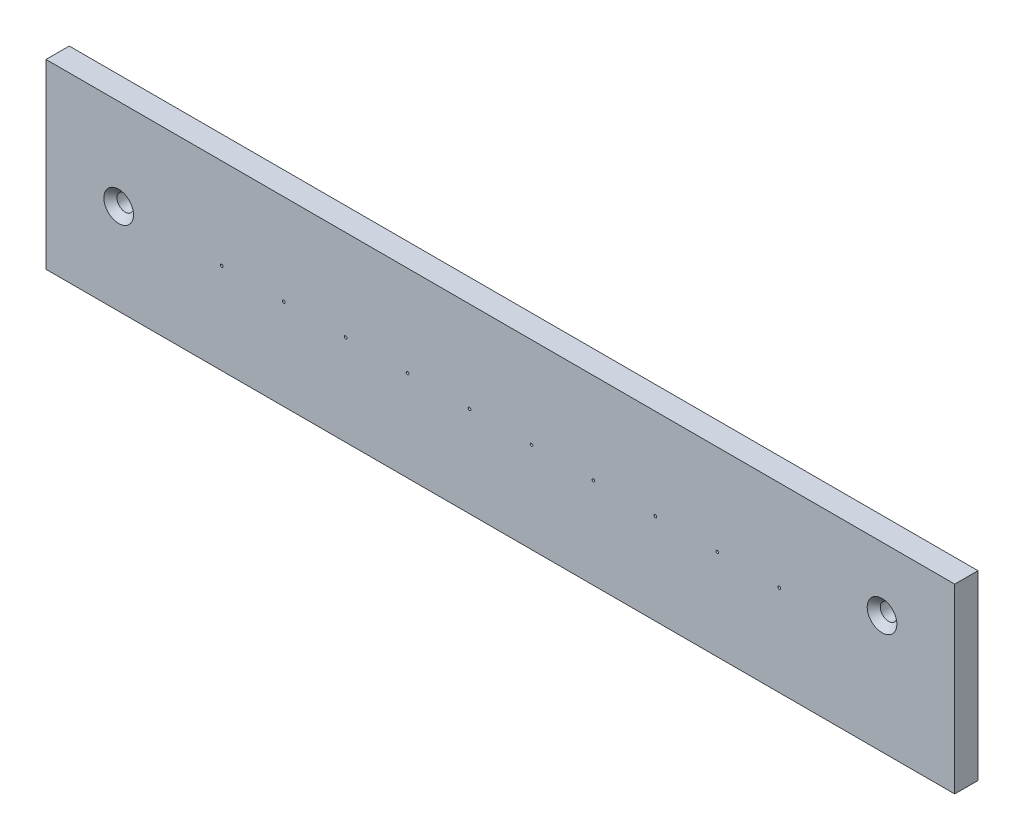
SolidWorks part; units mm, degrees
ref_plane "Front Plane" through (0, 0, 0) normal (0, 0, 1) x (1, 0, 0)
ref_plane "Top Plane" through (0, 0, 0) normal (0, 1, 0) x (1, 0, 0)
ref_plane "Right Plane" through (0, 0, 0) normal (1, 0, 0) x (0, 0, -1)
sketch "Sketch1" plane through (0, 0, 0) normal (0, 0, 1) x (1, 0, 0)
  line L1 (-31.6476, 20.0742) -> (127.1024, 20.0742)
  line L2 (-31.6476, 20.0742) -> (-31.6476, -11.6758)
  line L3 (-31.6476, -11.6758) -> (127.1024, -11.6758)
  line L4 (127.1024, 20.0742) -> (127.1024, -11.6758)
  dimension "D1" = 31.75
  dimension "D2" = 158.75
extrude "Boss-Extrude1" add sketch "Sketch1" against normal blind 4.064
sketch "Sketch2" plane through (0, 0, 0) normal (0, 0, 1) x (1, 0, 0)
  line L0 (-31.6476, 20.0742) -> (-31.6476, -11.6758) construction
  line L2 (127.1024, -11.6758) -> (127.1024, 20.0742) construction
  line L3 (127.1024, 20.0742) -> (-31.6476, 20.0742) construction
  circle A0 centre (-18.9476, 4.1992) radius 1.4478
  circle A1 centre (114.4024, 8.9617) radius 1.4478
  dimension "D1" = 2.8956
  dimension "D2" = 2.8956
  dimension "D3" = 12.7
  dimension "D4" = 12.7
  dimension "D5" = 11.1125
extrude "Cut-Extrude1" cut sketch "Sketch2" against normal through all
chamfer "Chamfer1" distance 1.143 angle 45 2 edges at (115.8502, 8.9617, 0) (-17.4998, 4.1992, 0)
sketch "Sketch4" plane through (0, 0, 0) normal (0, 0, 1) x (1, 0, 0)
  line L0 (-31.6476, 20.0742) -> (-31.6476, -11.6758) construction
  circle A0 centre (-0.939, 4.1992) radius 0.24
  point P4 (-31.6476, 4.1992)
  dimension "D2" = 0.4801
  dimension "D1" = 30.7086
extrude "Cut-Extrude2" cut sketch "Sketch4" against normal through all contours A0
pattern_linear "LPattern1" count 10 spacing 10.8204 along (1, 0, 0) of "Cut-Extrude2"
